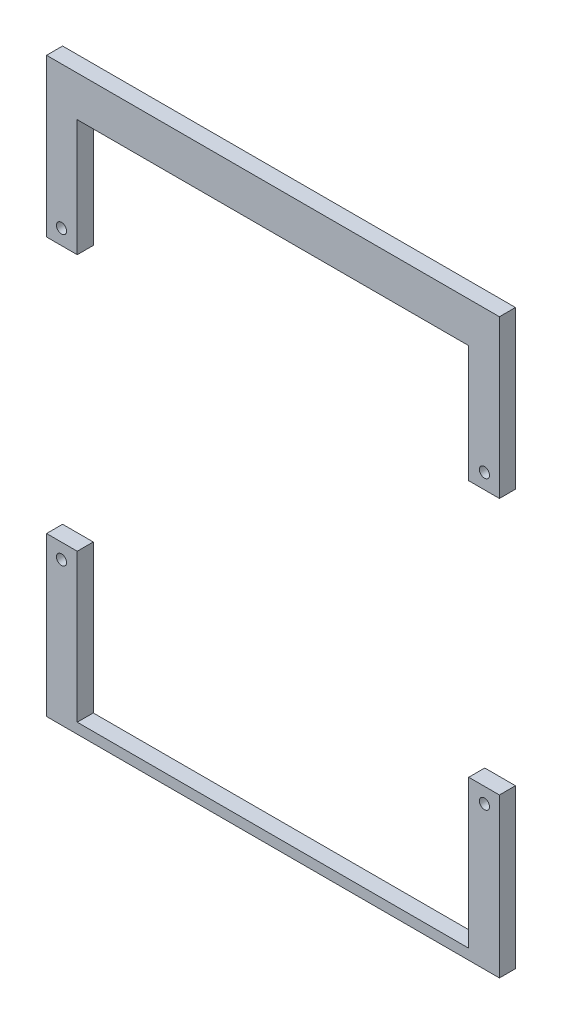
SolidWorks part; units mm, degrees
material "Neoprene Foam"
ref_plane "Front Plane" through (0, 0, 0) normal (0, 0, 1) x (1, 0, 0)
ref_plane "Top Plane" through (0, 0, 0) normal (0, 1, 0) x (1, 0, 0)
ref_plane "Right Plane" through (0, 0, 0) normal (1, 0, 0) x (0, 0, -1)
sketch "Sketch1" plane through (0, 0, 0) normal (0, 0, 1) x (1, 0, 0)
  line L0 (0, -107.43) -> (0, 119.3)
  line L1 (-77.5, 103.3) -> (77.5, 103.3)
  line L2 (-77.5, 103.3) -> (-77.5, -103.3)
  line L3 (-77.5, -103.3) -> (77.5, -103.3)
  line L4 (77.5, 103.3) -> (77.5, -103.3) construction
  line L5 (-77.5, 103.3) -> (77.5, -103.3) construction
  line L6 (-77.5, -103.3) -> (77.5, 103.3) construction
  line L7 (-89.6514, 119.3) -> (89.6514, 119.3)
  line L8 (-89.6514, 119.3) -> (-89.6514, -107.43)
  line L9 (-89.6514, -107.43) -> (89.6514, -107.43)
  line L10 (89.6514, 119.3) -> (89.6514, -107.43) construction
  line L11 (-83.72, -50.6724) -> (-83.72, 62.98) construction
  line L12 (-89.6514, 56.98) -> (-77.5, 56.98)
  line L13 (-77.5, -44.6724) -> (-89.6514, -44.6724)
  circle A0 centre (-83.72, 62.98) radius 2
  circle A1 centre (-83.72, -50.6724) radius 2
  point P0 (0, 0)
  point P6 (0, 0)
  dimension "D6" = 4
  dimension "D7" = 4
  dimension "D12" = 6
  dimension "D1" = 155
  dimension "D2" = 206.6
  dimension "D3" = 179.3028
  dimension "D4" = 4.13
  dimension "D5" = 16
  dimension "D8" = 170.41
  dimension "D9" = 56.7576
  dimension "D10" = 5.9314
  dimension "D11" = 6
extrude "Repeating Frame" add sketch "Sketch1" along normal blind 6.35 contours L2 L13 L8 L9 L0 L3 A1 | L8 L12 L2 L1 L0 L7 A0
mirror "Mirror1" about plane through (0, 0, 0) normal (1, 0, 0) of "Repeating Frame"
